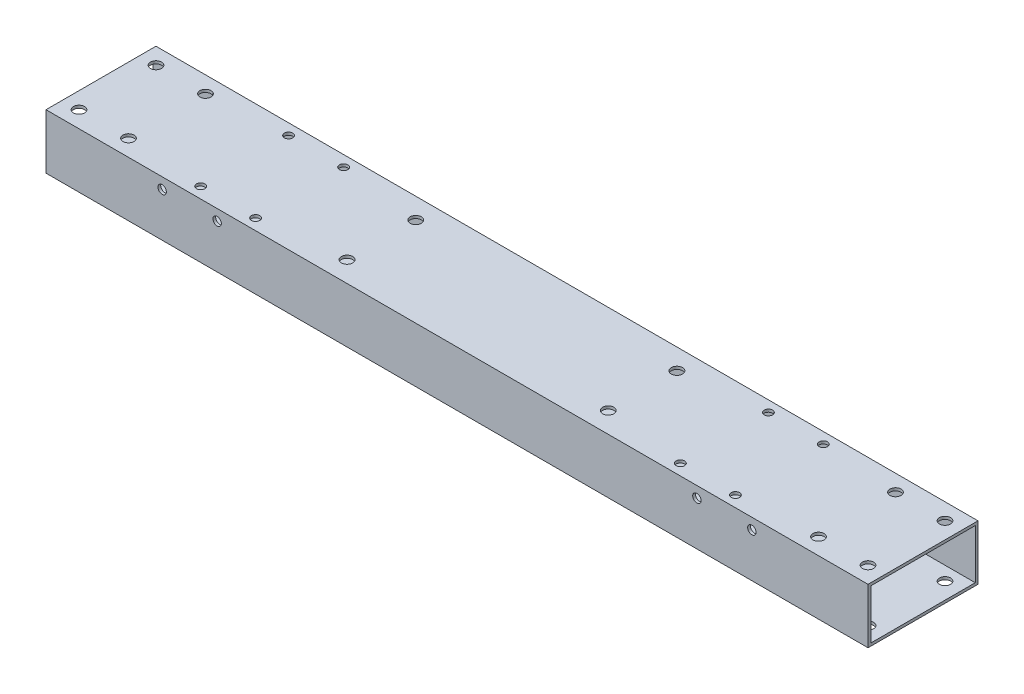
SolidWorks part; units mm, degrees
material "6063-T5"
ref_plane "前视基准面" through (0, 0, 0) normal (0, 0, 1) x (1, 0, 0)
ref_plane "上视基准面" through (0, 0, 0) normal (0, 1, 0) x (1, 0, 0)
ref_plane "右视基准面" through (0, 0, 0) normal (1, 0, 0) x (0, 0, -1)
other "Configuration Table"
sketch "草图1" plane through (0, 0, 0) normal (1, 0, 0) x (0, 0, -1)
  line L1 (-20, -10) -> (20, -10)
  line L2 (-20, -10) -> (-20, 10)
  line L3 (-20, 10) -> (20, 10)
  line L4 (20, -10) -> (20, 10)
  line L5 (-20, -10) -> (20, 10) construction
  line L6 (-20, 10) -> (20, -10) construction
  point P0 (0, 0)
  dimension "D1" = 20
  dimension "D2" = 40
extrude "凸台-拉伸1" add sketch "草图1" along normal mid plane 299
sketch "草图2" plane through (-149.5, 0, 0) normal (-1, 0, 0) x (0, 0, 1)
  line L8 (-19, 9) -> (-19, -9)
  line L9 (-19, -9) -> (19, -9)
  line L10 (19, -9) -> (19, 9)
  line L11 (19, 9) -> (-19, 9)
  line L12 (-19, 9) -> (-19, -9)
  line L13 (-19, -9) -> (19, -9)
  line L14 (19, -9) -> (19, 9)
  line L15 (19, 9) -> (-19, 9)
  dimension "D1" = 1
extrude "切除-拉伸1" cut sketch "草图2" against normal blind 2999
sketch "草图4" plane through (0, 10, 0) normal (0, 1, 0) x (1, 0, 0)
  line L1 (-47.5, 12.5) -> (47.5, 12.5) construction
  line L2 (-47.5, 12.5) -> (-47.5, -12.5) construction
  line L3 (-47.5, -12.5) -> (47.5, -12.5) construction
  line L4 (47.5, 12.5) -> (47.5, -12.5) construction
  circle A0 centre (-47.5, 12.5) radius 2.05
  circle A1 centre (-47.5, -12.5) radius 2.05
  circle A2 centre (47.5, 12.5) radius 2.05
  circle A3 centre (47.5, -12.5) radius 2.05
  point P8 (0, 12.5)
  point P10 (47.5, 0)
  dimension "D3" = 4.1
  dimension "D1" = 95
  dimension "D2" = 25
extrude "切除-拉伸2" cut sketch "草图4" against normal blind 2999
sketch "草图5" plane through (0, -10, 0) normal (0, -1, 0) x (1, 0, 0)
  line L0 (0, 0) -> (0, 20) construction
  line L1 (-143.5, -14) -> (-125.5, -14) construction
  line L2 (-143.5, -14) -> (-143.5, 14) construction
  line L3 (-143.5, 14) -> (-125.5, 14) construction
  line L4 (-125.5, -14) -> (-125.5, 14) construction
  line L5 (-143.5, -14) -> (-125.5, 14) construction
  line L6 (-143.5, 14) -> (-125.5, -14) construction
  line L7 (149.5, 20) -> (-149.5, 20) construction
  circle A0 centre (-125.5, 14) radius 2.025
  circle A1 centre (-125.5, -14) radius 2.025
  circle A2 centre (-143.5, -14) radius 2.025
  circle A3 centre (-143.5, 14) radius 2.025
  point P0 (-134.5, 0)
  dimension "D1" = 4.05
  dimension "D2" = 18
  dimension "D3" = 28
  dimension "D4" = 287
extrude "切除-拉伸3" cut sketch "草图5" against normal blind 2999
mirror "镜向1" about plane through (0, 0, 0) normal (1, 0, 0) of "切除-拉伸3"
sketch "草图6" plane through (0, 10, 0) normal (0, 1, 0) x (1, 0, 0)
  circle A0 centre (-97.25, 16) radius 1.525
  circle A1 centre (-97.25, -16) radius 1.525
  circle A2 centre (-77.25, -16) radius 1.525
  circle A3 centre (-77.25, 16) radius 1.525
  dimension "D1" = 3.05
extrude "切除-拉伸4" cut sketch "草图6" against normal through all both and the other way through all
sketch "草图8" plane through (0, 0, 20) normal (0, 0, 1) x (1, 0, 0)
  line L0 (-149.5, 10) -> (-149.5, -10) construction
  line L1 (149.5, 10) -> (-149.5, 10) construction
  circle A0 centre (-107.25, 6) radius 1.525
  circle A1 centre (-87.25, 6) radius 1.525
  dimension "D1" = 42.25
  dimension "D2" = 20
  dimension "D3" = 4
  dimension "D4" = 3.05
extrude "切除-拉伸5" cut sketch "草图8" against normal through all both
mirror "镜向2" about plane through (0, 0, 0) normal (1, 0, 0) of "切除-拉伸4", "切除-拉伸5"
